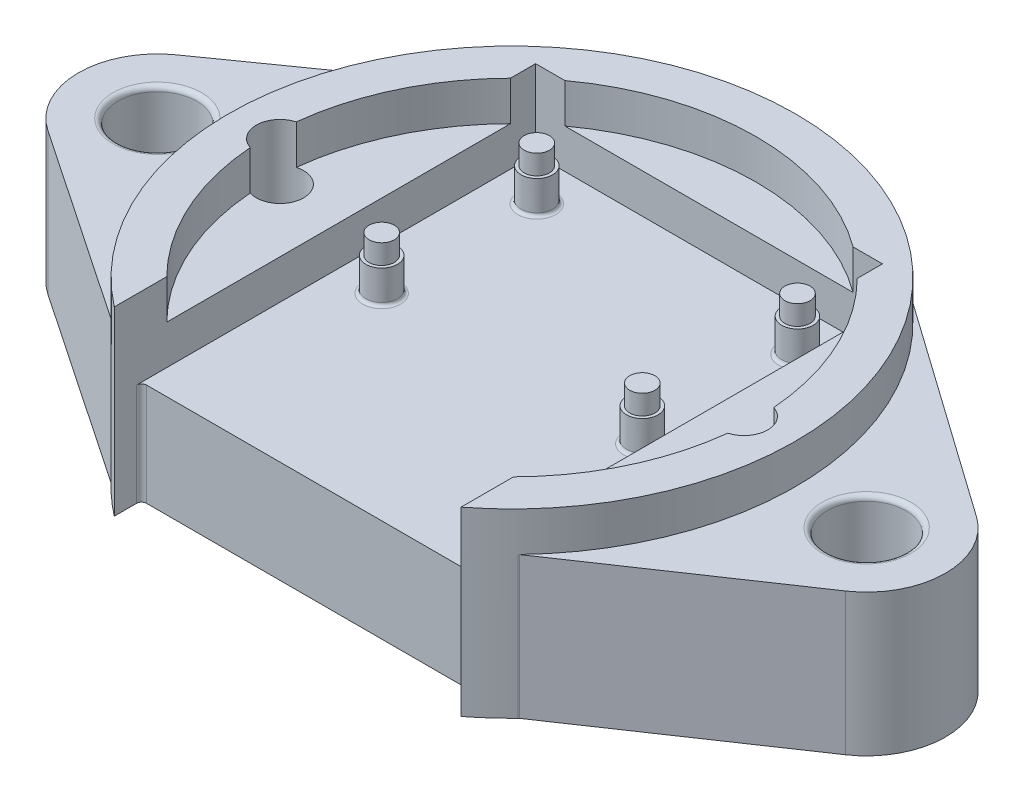
SolidWorks part; units mm, degrees
material "ABS"
ref_plane "Front Plane" through (0, 0, 0) normal (0, 0, 1) x (1, 0, 0)
ref_plane "Top Plane" through (0, 0, 0) normal (0, 1, 0) x (1, 0, 0)
ref_plane "Right Plane" through (0, 0, 0) normal (1, 0, 0) x (0, 0, -1)
sketch "Sketch1" plane through (0, 0, 0) normal (0, 1, 0) x (1, 0, 0)
  line L1 (-12.7, 12.7) -> (12.7, 12.7)
  line L2 (-12.7, 12.7) -> (-12.7, -12.7)
  line L4 (12.7, 12.7) -> (12.7, -12.7)
  line L5 (-12.7, 12.7) -> (12.7, -12.7) construction
  line L6 (-12.7, -12.7) -> (12.7, 12.7) construction
  line L9 (12.7, -12.7) -> (-12.7, -12.7)
  arc A0 (2.7738, -22.6744) -> (-3.5752, -22.5619) centre (0, 0) ccw construction
  circle A1 centre (0, 0) radius 22.8434
  dimension "D1" = 25.4
  dimension "D2" = 25.4
extrude "Boss-Extrude1" add sketch "Sketch1" against normal blind 3.175
sketch "Sketch3" plane through (0, 0, 0) normal (0, 1, 0) x (1, 0, 0)
  circle A0 centre (0, 0) radius 22.8434
  circle A1 centre (0, 0) radius 19.6684
  arc A2 (2.7738, -22.6744) -> (-3.5752, -22.5619) centre (0, 0) ccw construction
  arc A3 (-19.6129, -1.4766) -> (19.5483, -2.1704) centre (0, 0) ccw construction
extrude "Boss-Extrude2" add sketch "Sketch3" along normal blind 3.175 contours A0 | A1
sketch "Sketch4" plane through (0, -3.175, 0) normal (0, -1, 0) x (1, 0, 0)
  circle A0 centre (0, 0) radius 22.8434 construction
  circle A1 centre (0, 0) radius 22.8434
extrude "Boss-Extrude3" add sketch "Sketch4" along normal blind 3.175
sketch "Sketch14" plane through (0, 0, 0) normal (0, 1, 0) x (1, 0, 0)
  line L1 (-12.7, 15.875) -> (12.7, 15.875)
  line L2 (-12.7, 15.875) -> (-12.7, 12.7)
  line L3 (-12.7, 12.7) -> (12.7, 12.7)
  line L4 (12.7, 15.875) -> (12.7, 12.7)
  line L5 (-12.7, 15.875) -> (12.7, 12.7) construction
  line L6 (-12.7, 12.7) -> (12.7, 15.875) construction
  point P0 (0, 14.2875)
  dimension "D1" = 3.175
extrude "Cut-Extrude5" cut sketch "Sketch14" along normal blind 3.175 and the other way blind 3.175 contours L1 L4 L3 L2
sketch "Sketch18" plane through (0, 0, 0) normal (0, 1, 0) x (1, 0, 0)
  line L0 (-11.6117, 15.875) -> (11.6117, 15.875) construction
  line L1 (-13.97, 15.875) -> (13.97, 15.875)
  line L2 (-13.97, 15.875) -> (-13.97, -15.875)
  line L3 (-13.97, -15.875) -> (13.97, -15.875)
  line L4 (13.97, 15.875) -> (13.97, -15.875)
  line L5 (-13.97, 15.875) -> (13.97, -15.875) construction
  line L6 (-13.97, -15.875) -> (13.97, 15.875) construction
  point P0 (0, 0)
  dimension "D1" = 27.94
extrude "Cut-Extrude7" cut sketch "Sketch18" against normal up to surface (3.175 mm away) and the other way through all up to face at (0, -3.175, -1.5875)
sketch "Sketch7" plane through (0, 3.175, 0) normal (0, 1, 0) x (1, 0, 0)
  line L0 (13.97, -13.845) -> (13.97, 13.845) construction
  line L1 (-13.97, -15.875) -> (13.97, -15.875)
  line L2 (-13.97, -15.875) -> (-13.97, -41.275)
  line L3 (-13.97, -41.275) -> (13.97, -41.275)
  line L4 (13.97, -15.875) -> (13.97, -41.275)
  line L5 (-13.97, -15.875) -> (13.97, -41.275) construction
  line L6 (-13.97, -41.275) -> (13.97, -15.875) construction
  line L7 (-13.97, 13.845) -> (-13.97, -13.845) construction
  line L8 (-11.6117, -15.875) -> (11.6117, -15.875) construction
  point P0 (0, -28.575)
  dimension "D1" = 25.4
extrude "Cut-Extrude1" cut sketch "Sketch7" against normal through all
sketch "Sketch9" plane through (0, -3.175, 0) normal (0, 1, 0) x (1, 0, 0)
  circle A0 centre (-10.5, 12.5) radius 1.27
  circle A1 centre (10.5, 12.5) radius 1.27
  circle A2 centre (10.5, 0) radius 1.27
  circle A3 centre (-10.5, 0) radius 1.27
  circle A4 centre (-10.5, 12.5) radius 1.05 construction
  circle A8 centre (-10.5, 0) radius 1.05 construction
  circle A9 centre (10.5, 12.5) radius 1.05 construction
  dimension "D1" = 2.54
extrude "Boss-Extrude4" add sketch "Sketch9" along normal up to surface (2.654 mm away)
sketch "Sketch12" plane through (0, 3.175, 0) normal (0, 1, 0) x (1, 0, 0)
  line L0 (-19.0304, 0.3371) -> (0, 0) construction
  line L1 (0, 0) -> (19.0304, -0.3371) construction
  circle A0 centre (-19.0304, 0.3371) radius 1.905
  circle A1 centre (19.0304, -0.3371) radius 1.905
  circle A2 centre (19.0304, -0.3371) radius 1.905 construction
  circle A3 centre (-19.0304, 0.3371) radius 1.905 construction
extrude "Cut-Extrude3" cut sketch "Sketch12" against normal through all both and the other way through all
sketch "Sketch15" plane through (0, -6.35, 0) normal (0, -1, 0) x (1, 0, 0)
  line L0 (-16.4258, 15.875) -> (-32.1307, 5.2612)
  line L1 (-13.1851, -18.654) -> (-32.2402, -5.1854)
  line L2 (0, 15.875) -> (0, -22.8434) construction
  line L3 (-13.97, 15.875) -> (13.97, 15.875) construction
  line L4 (13.1851, -18.654) -> (32.2402, -5.1854)
  line L5 (16.4258, 15.875) -> (32.1307, 5.2612)
  line L6 (-13.97, 15.875) -> (13.97, 15.875) construction
  arc A0 (-13.97, 18.0737) -> (13.97, 18.0737) centre (0, 0) ccw construction
  arc A1 (-32.1307, 5.2612) -> (-32.2402, -5.1854) centre (-28.575, 0) ccw
  circle A2 centre (-28.575, 0) radius 3.175
  circle A3 centre (28.575, 0) radius 3.175
  arc A4 (32.1307, 5.2612) -> (32.2402, -5.1854) centre (28.575, 0) cw
  arc A5 (-13.97, 18.0737) -> (13.97, 18.0737) centre (0, 0) ccw construction
  arc M6 (-13.97, 18.0737) -> (13.97, 18.0737) centre (0, 0) ccw
  dimension "D1" = 6.35
  dimension "D3" = 3.175
  dimension "D2" = 28.575
extrude "Boss-Extrude5" add sketch "Sketch15" against normal blind 6.35 contours A4 L5 L4 A3 M6 | L0 A1 L1 A2 M6
sketch "Sketch17" plane through (0, -6.35, 0) normal (0, -1, 0) x (1, 0, 0)
  line L0 (-13.97, 15.875) -> (13.97, 15.875) construction
  line L2 (-16.4258, 15.875) -> (-32.1307, 5.2612) construction
  line L3 (-13.1851, -18.654) -> (-32.2402, -5.1854) construction
  line L4 (13.1851, -18.654) -> (32.2402, -5.1854) construction
  line L5 (16.4258, 15.875) -> (32.1307, 5.2612) construction
  line L7 (-13.97, 15.875) -> (13.97, 15.875)
  line L8 (-13.97, 15.875) -> (-13.97, 18.0737)
  line L9 (-16.4258, 15.875) -> (-32.1307, 5.2612)
  line L10 (-13.1851, -18.654) -> (-32.2402, -5.1854)
  line L11 (13.1851, -18.654) -> (32.2402, -5.1854)
  line L12 (16.4258, 15.875) -> (32.1307, 5.2612)
  line L13 (13.97, 15.875) -> (13.97, 18.0737)
  circle A0 centre (-28.575, 0) radius 3.175 construction
  arc A1 (-13.97, 18.0737) -> (-16.4258, 15.875) centre (0, 0) ccw construction
  arc A2 (-32.1307, 5.2612) -> (-32.2402, -5.1854) centre (-28.575, 0) ccw construction
  arc A3 (-13.1851, -18.654) -> (13.1851, -18.654) centre (0, 0) ccw construction
  circle A4 centre (28.575, 0) radius 3.175 construction
  arc A5 (32.2402, -5.1854) -> (32.1307, 5.2612) centre (28.575, 0) ccw construction
  arc A6 (16.4258, 15.875) -> (13.97, 18.0737) centre (0, 0) ccw construction
  circle A7 centre (-28.575, 0) radius 3.175
  arc A8 (-13.97, 18.0737) -> (-16.4258, 15.875) centre (0, 0) ccw
  arc A9 (-32.1307, 5.2612) -> (-32.2402, -5.1854) centre (-28.575, 0) ccw
  arc A10 (-13.1851, -18.654) -> (13.1851, -18.654) centre (0, 0) ccw
  circle A11 centre (28.575, 0) radius 3.175
  arc A12 (32.2402, -5.1854) -> (32.1307, 5.2612) centre (28.575, 0) ccw
  arc A13 (16.4258, 15.875) -> (13.97, 18.0737) centre (0, 0) ccw
extrude "Boss-Extrude6" add sketch "Sketch17" along normal blind 5.08
sketch "Sketch16" plane through (0, -11.43, 0) normal (0, -1, 0) x (-1, 0, 0)
  line L1 (13.8978, 0.3371) -> (16.4641, -4.1079)
  line L2 (16.4641, -4.1079) -> (21.5967, -4.1079)
  line L3 (21.5967, -4.1079) -> (24.1631, 0.3371)
  line L4 (24.1631, 0.3371) -> (21.5967, 4.7821)
  line L5 (21.5967, 4.7821) -> (16.4641, 4.7821)
  line L6 (16.4641, 4.7821) -> (13.8978, 0.3371)
  line L7 (-16.4641, 4.1079) -> (-21.5967, 4.1079)
  line L8 (-21.5967, 4.1079) -> (-24.1631, -0.3371)
  line L9 (-24.1631, -0.3371) -> (-21.5967, -4.7821)
  line L10 (-21.5967, -4.7821) -> (-16.4641, -4.7821)
  line L11 (-16.4641, -4.7821) -> (-13.8978, -0.3371)
  line L12 (-13.8978, -0.3371) -> (-16.4641, 4.1079)
  circle A0 centre (19.0304, 0.3371) radius 4.445 construction
  circle A1 centre (-19.0304, -0.3371) radius 4.445 construction
  dimension "D1" = 8.89
extrude "Cut-Extrude6" cut sketch "Sketch16" against normal blind 5.08
fillet "Fillet1" radius 0.254 4 edges at (-10.5, -3.175, -1.27) (-10.5, -3.175, -13.77) (10.5, -3.175, -13.77) (10.5, -3.175, -1.27)
fillet "Fillet2" radius 0.3969 6 edges at (-16.4258, -5.715, 15.875) (-13.97, -7.3025, 15.875) (13.97, -7.3025, 15.875) (16.4258, -5.715, 15.875) (28.575, 0, -3.175) (-28.575, 0, -3.175)
chamfer "Chamfer2" distance 0.3175 angle 80 12 edges at (-22.8799, -11.43, 1.8854) (-22.8799, -11.43, -2.5596) (-19.0304, -11.43, -4.7821) (-15.1809, -11.43, -2.5596) (-19.0304, -11.43, 4.1079) (-15.1809, -11.43, 1.8854) (22.8799, -11.43, 2.5596) (19.0304, -11.43, 4.7821) (15.1809, -11.43, 2.5596) (15.1809, -11.43, -1.8854) (19.0304, -11.43, -4.1079) (22.8799, -11.43, -1.8854)
sketch "Sketch20" plane through (0, -0.521, 0) normal (0, 1, 0) x (1, 0, 0)
  circle A0 centre (10.5, 12.5) radius 1.016
  circle A1 centre (10.5, 0) radius 1.016
  circle A2 centre (-10.5, 0) radius 1.016
  circle A3 centre (-10.5, 12.5) radius 1.016
  dimension "D1" = 2.032
extrude "Boss-Extrude8" add sketch "Sketch20" along normal blind 1.5875
